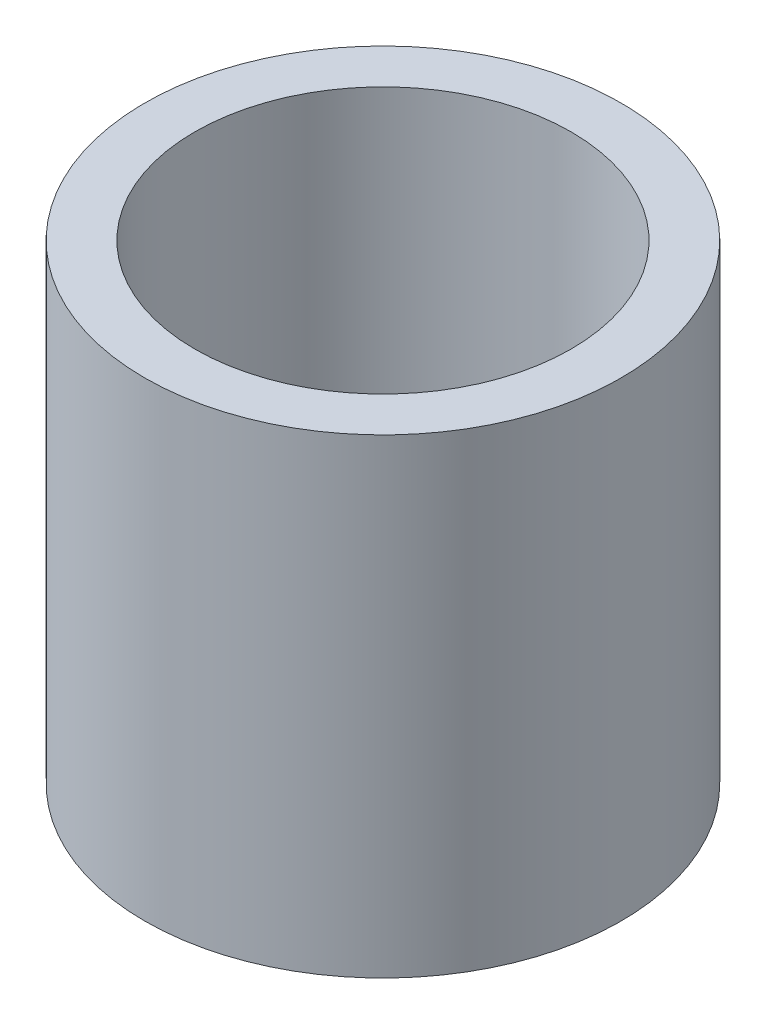
SolidWorks part; units mm, degrees
ref_plane "Front Plane" through (0, 0, 0) normal (0, 0, 1) x (1, 0, 0)
ref_plane "Top Plane" through (0, 0, 0) normal (0, 1, 0) x (1, 0, 0)
ref_plane "Right Plane" through (0, 0, 0) normal (1, 0, 0) x (0, 0, -1)
sketch "Sketch1" plane through (0, 0, 0) normal (0, 1, 0) x (1, 0, 0)
  circle A0 centre (0, 0) radius 7.9
  circle A1 centre (0, 0) radius 10
  dimension "D1" = 15.8
  dimension "D2" = 20
extrude "Boss-Extrude1" add sketch "Sketch1" along normal blind 19.75
equation "\"8mm hole\" = 8.4mm'used to be the diameter of the linear motion rods"
equation "\"22mm hole\"= 23mm'this is the size of the hole for the nema 17 standard was 22mm"
equation "\"15mm hole\"= 15.8mm'this is the hole for the linear motion sliders, they are all set to this measurement so if you have different sized bearing sliders you may have to adjust individually"
equation "\"D1@Sketch1\"= \"15mm hole\""
